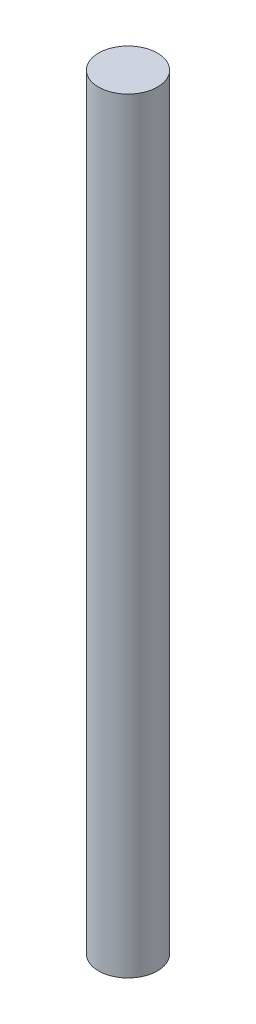
SolidWorks part; units mm, degrees
material "AISI 1020"
ref_plane "Front Plane" through (0, 0, 0) normal (0, 0, 1) x (1, 0, 0)
ref_plane "Top Plane" through (0, 0, 0) normal (0, 1, 0) x (1, 0, 0)
ref_plane "Right Plane" through (0, 0, 0) normal (1, 0, 0) x (0, 0, -1)
sketch "Sketch1" plane through (0, 0, 0) normal (0, 1, 0) x (1, 0, 0)
  circle A0 centre (0, 0) radius 6.35
  dimension "D1" = 12.7
extrude "Boss-Extrude1" add sketch "Sketch1" along normal blind 165
